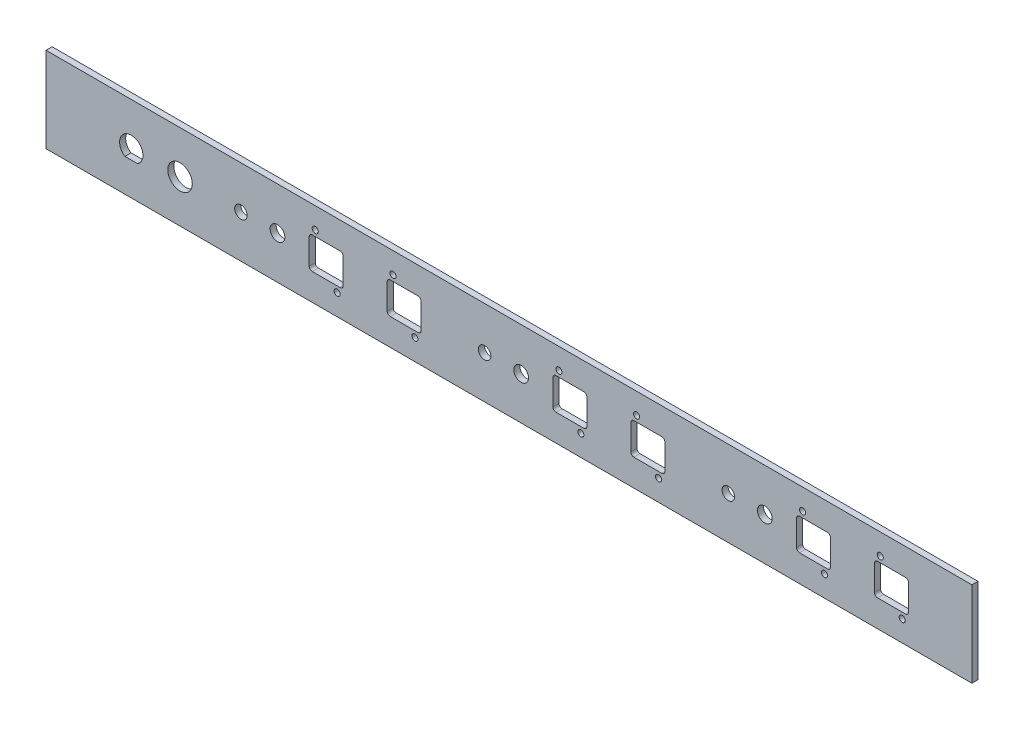
SolidWorks part; units mm, degrees
material "6061-T6 (SS)"
ref_plane "Front Plane" through (0, 0, 0) normal (0, 0, 1) x (1, 0, 0)
ref_plane "Top Plane" through (0, 0, 0) normal (0, 1, 0) x (1, 0, 0)
ref_plane "Right Plane" through (0, 0, 0) normal (1, 0, 0) x (0, 0, -1)
sketch "Sketch1" plane through (0, 0, 0) normal (0, 0, 1) x (1, 0, 0)
  line L1 (-241.3, 22.225) -> (241.3, 22.225)
  line L2 (-241.3, 22.225) -> (-241.3, -22.225)
  line L3 (-241.3, -22.225) -> (241.3, -22.225)
  line L4 (241.3, 22.225) -> (241.3, -22.225)
  line L5 (-241.3, 22.225) -> (241.3, -22.225) construction
  line L6 (-241.3, -22.225) -> (241.3, 22.225) construction
  point P0 (0, 0)
  dimension "D1" = 482.6
  dimension "D2" = 44.45
extrude "Boss-Extrude1" add sketch "Sketch1" along normal blind 3.175
sketch "Sketch2" plane through (0, 0, 3.175) normal (0, 0, 1) x (1, 0, 0)
  line L1 (-215.9, 20.6375) -> (215.9, 20.6375) construction
  line L2 (-215.9, 20.6375) -> (-215.9, -20.6375) construction
  line L3 (-215.9, -20.6375) -> (215.9, -20.6375) construction
  line L4 (215.9, 20.6375) -> (215.9, -20.6375) construction
  line L5 (-215.9, 20.6375) -> (215.9, -20.6375) construction
  line L6 (-215.9, -20.6375) -> (215.9, 20.6375) construction
  point P0 (0, 0)
  dimension "D1" = 431.8
  dimension "D2" = 41.275
sketch "Sketch4" plane through (0, 0, 3.175) normal (0, 0, 1) x (1, 0, 0)
  line L0 (-200.1811, -5.1054) -> (-193.5189, -5.1054)
  arc A0 (-193.5189, -5.1054) -> (-200.1811, -5.1054) centre (-196.85, 0) ccw
  circle A1 centre (-171.45, 0) radius 6.3881
  dimension "D1" = 12.192
  dimension "D3" = 12.7762
  dimension "D2" = 11.2014
  dimension "D4" = 25.4
  dimension "D5" = 196.85
extrude "Cut-Extrude1" cut sketch "Sketch4" against normal through all
sketch "Sketch3" plane through (0, 0, 3.175) normal (0, 0, 1) x (1, 0, 0)
  line L1 (-104.1146, 8.255) -> (-86.3854, 8.255)
  line L2 (-104.1146, 8.255) -> (-104.1146, -8.255)
  line L3 (-104.1146, -8.255) -> (-86.3854, -8.255)
  line L4 (-86.3854, 8.255) -> (-86.3854, -8.255)
  line L5 (-104.1146, 8.255) -> (-86.3854, -8.255) construction
  line L6 (-104.1146, -8.255) -> (-86.3854, 8.255) construction
  line L7 (-63.4746, 8.255) -> (-45.7454, 8.255)
  line L8 (-63.4746, 8.255) -> (-63.4746, -8.255)
  line L9 (-63.4746, -8.255) -> (-45.7454, -8.255)
  line L10 (-45.7454, 8.255) -> (-45.7454, -8.255)
  line L11 (-63.4746, 8.255) -> (-45.7454, -8.255) construction
  line L12 (-63.4746, -8.255) -> (-45.7454, 8.255) construction
  circle A0 centre (-120.65, 0) radius 3.85
  circle A1 centre (-139.7, 0) radius 3.2512
  circle A2 centre (-100.965, 11.303) radius 1.5875
  circle A3 centre (-89.535, -11.303) radius 1.5875
  circle A4 centre (-60.452, 11.303) radius 1.5875
  circle A5 centre (-49.022, -11.303) radius 1.5875
  point P6 (-95.25, 0)
  point P16 (-54.61, 0)
  dimension "D1" = 7.7
  dimension "D2" = 6.5024
  dimension "D7" = 3.175
  dimension "D3" = 19.05
  dimension "D4" = 16.51
  dimension "D5" = 17.7292
  dimension "D6" = 11.43
  dimension "D8" = 22.606
  dimension "D9" = 11.303
  dimension "D10" = 5.715
  dimension "D11" = 25.4
  dimension "D12" = 3.0226
  dimension "D13" = 11.43
  dimension "D14" = 40.64
  dimension "D15" = 139.7
extrude "Cut-Extrude2" cut sketch "Sketch3" against normal through all
fillet "Fillet1" radius 1.6002 8 edges at (-63.4746, 8.255, 1.5875) (-63.4746, -8.255, 1.5875) (-86.3854, -8.255, 1.5875) (-45.7454, -8.255, 1.5875) (-45.7454, 8.255, 1.5875) (-86.3854, 8.255, 1.5875) (-104.1146, 8.255, 1.5875) (-104.1146, -8.255, 1.5875)
pattern_linear "LPattern1" count 3 spacing 127 along (1, 0, 0) of "Cut-Extrude2", "Fillet1"
